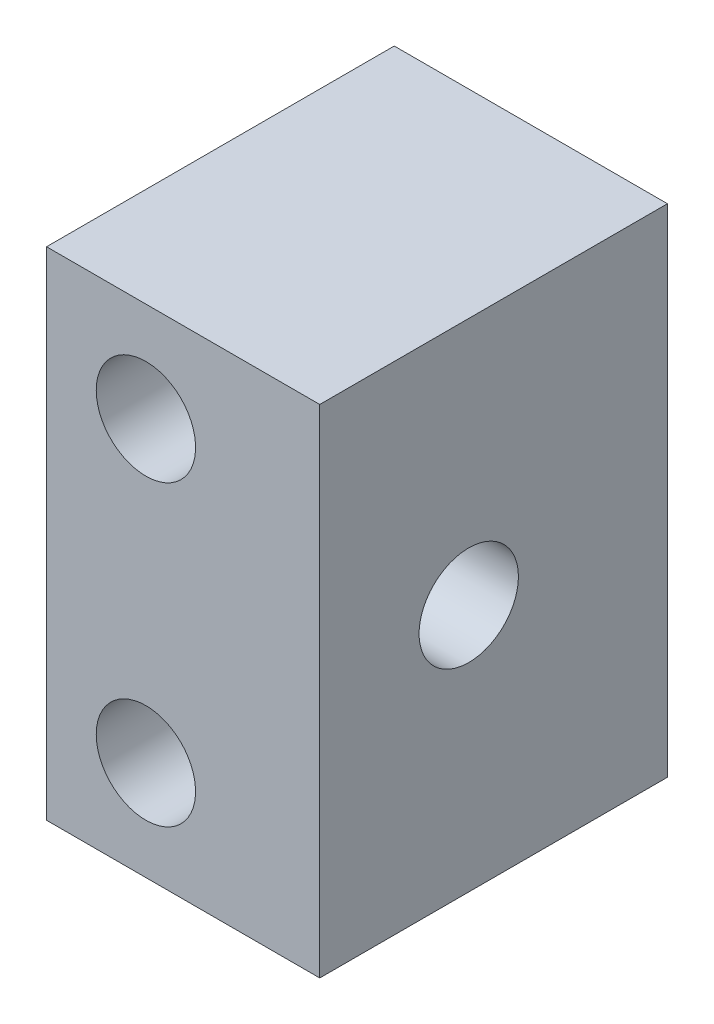
SolidWorks part; units mm, degrees
ref_plane "前视基准面" through (0, 0, 0) normal (0, 0, 1) x (1, 0, 0)
ref_plane "上视基准面" through (0, 0, 0) normal (0, 1, 0) x (1, 0, 0)
ref_plane "右视基准面" through (0, 0, 0) normal (1, 0, 0) x (0, 0, -1)
sketch "Model" plane through (0, 0, 0) normal (0, 0, 1) x (1, 0, 0)
  line L0 (199.4993, 238.6656) -> (199.4993, 228.6656)
  line L1 (199.4993, 238.6656) -> (193.9993, 238.6656)
  line L2 (195.9993, 234.6656) -> (197.4993, 234.6656)
  line L3 (193.9993, 238.6656) -> (193.9993, 234.6656)
  line L4 (194.9993, 234.6656) -> (195.9993, 234.6656)
  line L5 (199.4993, 228.6656) -> (193.9993, 228.6656)
  line L6 (195.9993, 232.6656) -> (197.4993, 232.6656)
  line L7 (193.9993, 228.6656) -> (193.9993, 232.6656)
  line L8 (194.9993, 232.6656) -> (195.9993, 232.6656)
  line L9 (197.4993, 234.6656) -> (197.4993, 232.6656)
  line L10 (194.9993, 234.6656) -> (194.9993, 232.6656)
  line L11 (193.9993, 234.6656) -> (193.9993, 232.6656)
  circle A0 centre (195.9993, 236.6656) radius 1
  circle A1 centre (195.9993, 230.6656) radius 1
extrude "凸台-拉伸1" add sketch "Model" along normal blind 4 contours A1 | A0 | L2 L9 L6 L8 L10 L4 | L0 L5 L7 L11 L3 L1
sketch "草图1" plane through (197.4993, 0, 0) normal (-1, 0, 0) x (0, 0, 1)
  circle A0 centre (2, 233.6656) radius 1
extrude "切除-拉伸1" cut sketch "草图1" against normal blind 3 and the other way blind 5
sketch "草图2" plane through (193.9993, 0, 0) normal (-1, 0, 0) x (0, 0, 1)
  circle A0 centre (2, 233.6656) radius 1.9
extrude "切除-拉伸2" cut sketch "草图2" against normal blind 3.5
sketch "草图3" plane through (0, 0, 0) normal (0, 0, -1) x (-1, 0, 0)
sketch "草图4" plane through (0, 0, 0) normal (0, 0, -1) x (-1, 0, 0)
  line L4 (-193.9993, 238.6656) -> (-199.4993, 238.6656)
  line L5 (-199.4993, 238.6656) -> (-199.4993, 228.6656)
  line L6 (-199.4993, 228.6656) -> (-193.9993, 228.6656)
  line L7 (-193.9993, 228.6656) -> (-193.9993, 238.6656)
  line L8 (-193.9993, 238.6656) -> (-199.4993, 238.6656)
  line L9 (-199.4993, 238.6656) -> (-199.4993, 228.6656)
  line L10 (-199.4993, 228.6656) -> (-193.9993, 228.6656)
  line L11 (-193.9993, 228.6656) -> (-193.9993, 238.6656)
  dimension "D1" = 0
extrude "凸台-拉伸2" add sketch "草图4" along normal blind 2
sketch "草图5" plane through (0, 0, 0) normal (0, 0, 1) x (1, 0, 0)
  circle A1 centre (195.9993, 236.6656) radius 1
  circle A2 centre (195.9993, 236.6656) radius 1
  circle A3 centre (195.9993, 230.6656) radius 1
  circle A4 centre (195.9993, 230.6656) radius 1
  dimension "D1" = 0
  dimension "D2" = 0
extrude "切除-拉伸3" cut sketch "草图5" against normal blind 2 contours A2
sketch "草图6" plane through (0, 0, 0) normal (0, 0, 1) x (1, 0, 0)
  circle A1 centre (195.9993, 230.6656) radius 1
  circle A2 centre (195.9993, 230.6656) radius 1
  dimension "D1" = 0
extrude "切除-拉伸4" cut sketch "草图6" against normal blind 2
sketch "草图7" plane through (0, 0, 4) normal (0, 0, 1) x (1, 0, 0)
  line L4 (199.4993, 238.6656) -> (193.9993, 238.6656)
  line L5 (193.9993, 238.6656) -> (193.9993, 228.6656)
  line L6 (193.9993, 228.6656) -> (199.4993, 228.6656)
  line L7 (199.4993, 228.6656) -> (199.4993, 238.6656)
  line L8 (199.4993, 238.6656) -> (193.9993, 238.6656)
  line L9 (193.9993, 238.6656) -> (193.9993, 228.6656)
  line L10 (193.9993, 228.6656) -> (199.4993, 228.6656)
  line L11 (199.4993, 228.6656) -> (199.4993, 238.6656)
  dimension "D1" = 0
extrude "凸台-拉伸3" add sketch "草图7" along normal blind 1
sketch "草图8" plane through (0, 0, 4) normal (0, 0, -1) x (-1, 0, 0)
  circle A0 centre (-195.9993, 236.6656) radius 1 construction
  circle A1 centre (-195.9993, 230.6656) radius 1 construction
  circle A2 centre (-195.9993, 236.6656) radius 1
  circle A3 centre (-195.9993, 230.6656) radius 1
extrude "切除-拉伸5" cut sketch "草图8" against normal blind 1
